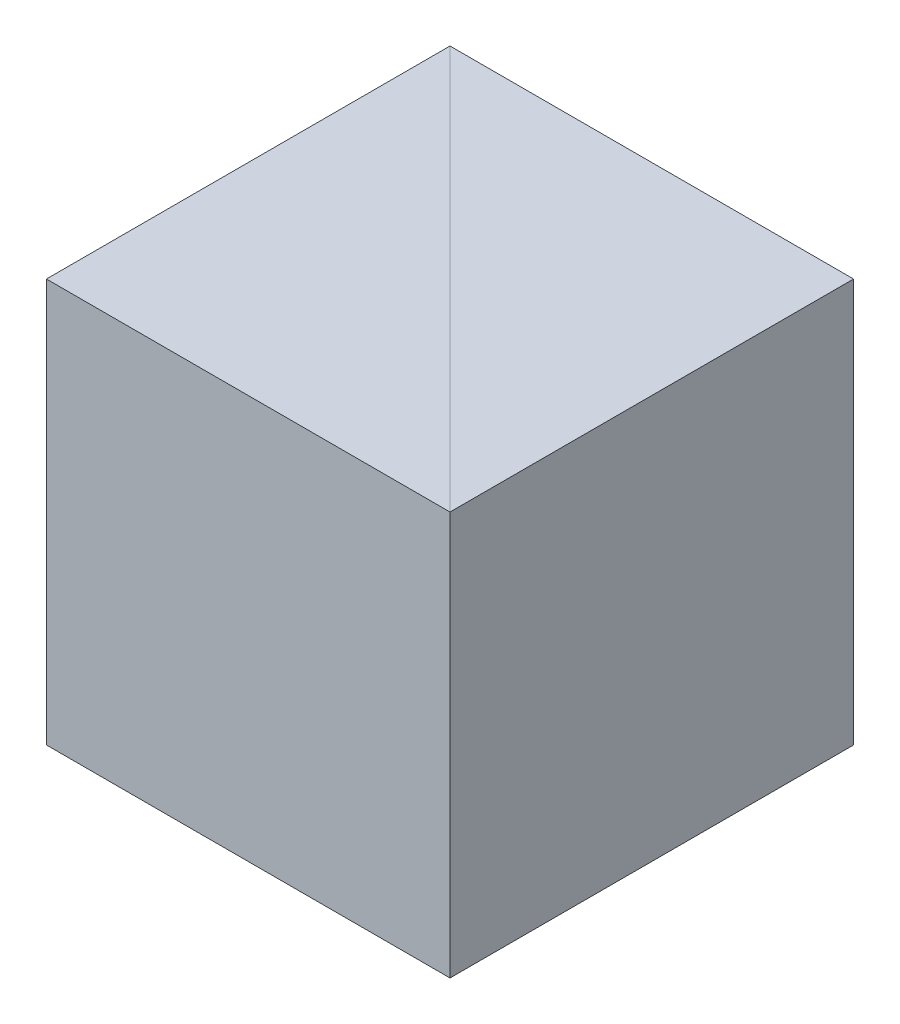
SolidWorks part; units mm, degrees
ref_plane "前视基准面" through (0, 0, 0) normal (0, 0, 1) x (1, 0, 0)
ref_plane "上视基准面" through (0, 0, 0) normal (0, 1, 0) x (1, 0, 0)
ref_plane "右视基准面" through (0, 0, 0) normal (1, 0, 0) x (0, 0, -1)
sketch "草图1" plane through (0, 0, 0) normal (0, 1, 0) x (1, 0, 0)
  line L0 (0, 0) -> (0, 25)
  line L1 (0, 25) -> (-25, 25)
  line L2 (-25, 25) -> (0, 0)
  dimension "D1" = 25
  dimension "D2" = 25
extrude "凸台-拉伸1" add sketch "草图1" along normal blind 25
sketch "草图2" plane through (0, 0, 0) normal (0, -1, 0) x (1, 0, 0)
  line L0 (-25, -25) -> (-25, 0)
  line L1 (-25, 0) -> (0, 0)
  line L2 (0, 0) -> (-25, -25)
extrude "凸台-拉伸2" add sketch "草图2" against normal blind 25 separate body
